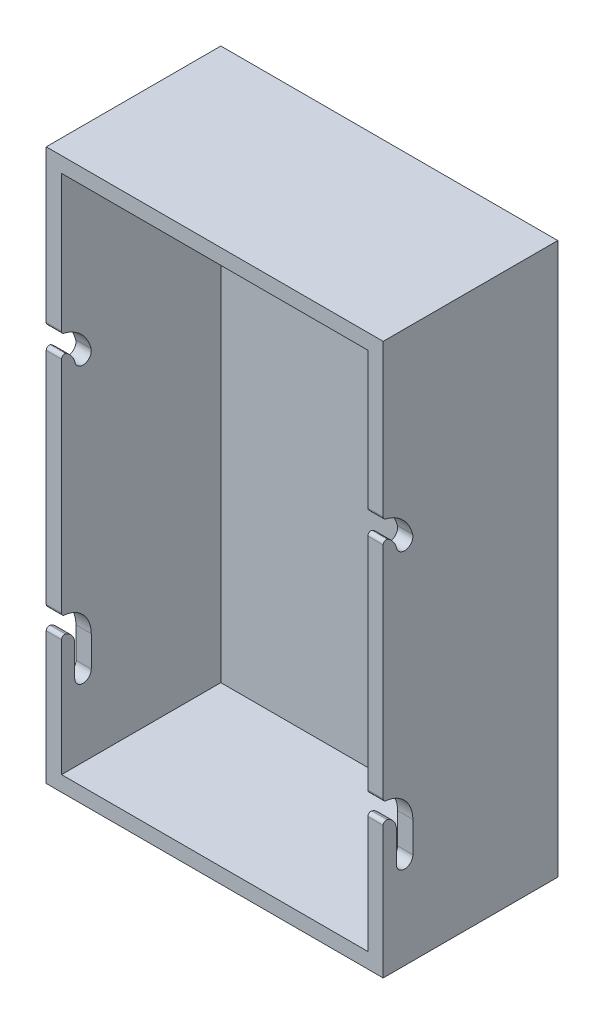
SolidWorks part; units mm, degrees
ref_plane "Plan de face" through (0, 0, 0) normal (0, 0, 1) x (1, 0, 0)
ref_plane "Plan de dessus" through (0, 0, 0) normal (0, 1, 0) x (1, 0, 0)
ref_plane "Plan de droite" through (0, 0, 0) normal (1, 0, 0) x (0, 0, -1)
sketch "Esquisse1" plane through (0, 0, 0) normal (0, 0, 1) x (1, 0, 0)
  line L1 (0, 0) -> (110, 0)
  line L2 (0, 0) -> (0, 180)
  line L3 (0, 180) -> (110, 180)
  line L4 (110, 0) -> (110, 180)
  line L5 (5, 5) -> (105, 5)
  line L6 (5, 5) -> (5, 175)
  line L7 (5, 175) -> (105, 175)
  line L8 (105, 5) -> (105, 175)
  dimension "D1" = 170
  dimension "D2" = 100
  dimension "D3" = 5
  dimension "D4" = 5
  dimension "D5" = 5
  dimension "D6" = 5
extrude "Boss.-Extru.1" add sketch "Esquisse1" along normal blind 57
sketch "Esquisse2" plane through (0, 0, 0) normal (0, 0, -1) x (-1, 0, 0)
  line L1 (-110, 180) -> (0, 180)
  line L2 (-110, 180) -> (-110, 0)
  line L3 (-110, 0) -> (0, 0)
  line L4 (0, 180) -> (0, 0)
extrude "Boss.-Extru.2" add sketch "Esquisse2" against normal blind 5
sketch "Esquisse3" plane through (0, 0, 0) normal (-1, 0, 0) x (0, 0, 1)
  line L0 (50, 40) -> (50, 30) construction
  line L1 (57, 180) -> (57, 0) construction
  line L2 (52.7, 40) -> (52.7, 30)
  line L3 (47.3, 40) -> (47.3, 30)
  line L5 (57, 0) -> (0, 0) construction
  arc A0 (57, 47) -> (50, 40) centre (57, 40) ccw construction
  arc A5 (57, 49.7) -> (47.3, 40) centre (57, 40) ccw
  arc A6 (57, 44.3) -> (52.7, 40) centre (57, 40) ccw
  arc A7 (57, 44.3) -> (57, 49.7) centre (57, 47) ccw
  arc A8 (47.3, 40) -> (52.7, 40) centre (50, 40) ccw
  arc A9 (52.7, 40) -> (47.3, 40) centre (50, 40) ccw
  arc A10 (47.3, 30) -> (52.7, 30) centre (50, 30) ccw
  arc A11 (57, 126.8) -> (50, 120) centre (58.9345, 117.8057) ccw construction
  arc A18 (56.4323, 129.4396) -> (47.3779, 120.644) centre (58.9345, 117.8057) ccw
  arc A19 (57.5677, 124.1604) -> (52.6221, 119.356) centre (58.9345, 117.8057) ccw
  arc A20 (57.5677, 124.1604) -> (56.4323, 129.4396) centre (57, 126.8) ccw
  arc A21 (47.3779, 120.644) -> (52.6221, 119.356) centre (50, 120) ccw
  point P3 (52.0503, 44.9497)
  point P10 (50, 35)
  point P22 (52.5241, 124.4047)
  line M12 (57, 0) -> (57, 180)
  dimension "D2" = 2.7
  dimension "D3" = 2.7
  dimension "D8" = 2.7
  dimension "D1" = 7
  dimension "D4" = 10
  dimension "D5" = 7
  dimension "D6" = 30
  dimension "D7" = 7
  dimension "D9" = 6.8
  dimension "D10" = 90
  dimension "D11" = 6.5
extrude "Enlèv. mat.-Extru.1" cut sketch "Esquisse3" against normal through all contours A18 A21 A19 A20 M12 | A19 A20 M12 | A9 A6 A5 M12 | A7 M12 | A8 A9 | L3 A10 L2 A8
fillet "Congé1" radius 1 8 edges at (2.5, 49.7, 57) (107.5, 49.7, 57) (107.5, 44.3, 57) (2.5, 44.3, 57) (2.5, 124.0111, 57) (2.5, 129.5, 57) (107.5, 124.0111, 57) (107.5, 129.5, 57)
